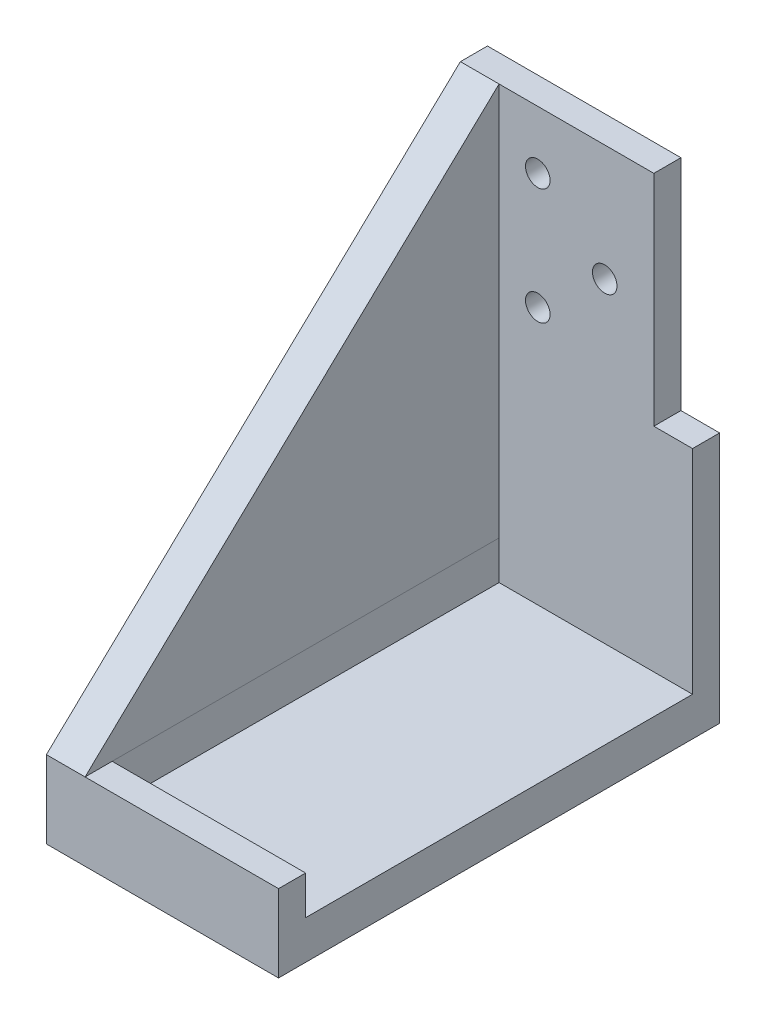
SolidWorks part; units mm, degrees
ref_plane "Front" through (0, 0, 0) normal (0, 0, 1) x (1, 0, 0)
ref_plane "Top" through (0, 0, 0) normal (0, 1, 0) x (1, 0, 0)
ref_plane "Right" through (0, 0, 0) normal (1, 0, 0) x (0, 0, -1)
sketch "Sketch1" plane through (0, 0, 0) normal (0, 1, 0) x (1, 0, 0)
  line L1 (-30, -57) -> (30, -57)
  line L2 (-30, -57) -> (-30, 57)
  line L3 (-30, 57) -> (30, 57)
  line L4 (30, -57) -> (30, 57)
  line L5 (-30, -57) -> (30, 57) construction
  line L6 (-30, 57) -> (30, -57) construction
  point P0 (0, 0)
  dimension "D1" = 60
  dimension "D2" = 114
extrude "Boss-Extrude1" add sketch "Sketch1" against normal blind 10
sketch "Sketch3" plane through (0, 0, 0) normal (0, 1, 0) x (1, 0, 0)
  line L1 (30, -57) -> (30, 57) construction
  line L5 (-30, 57) -> (30, 57)
  line L6 (30, 57) -> (-30, 57) construction
  line L7 (30, 57) -> (30, 50)
  line L8 (30, 50) -> (-30, 50)
  line L11 (-30, 50) -> (-30, 57)
  dimension "D1" = 7
extrude "Boss-Extrude2" add sketch "Sketch3" along normal offset from surface (111.6 mm away) 5
sketch "Sketch6" plane through (0, 0, 0) normal (0, 1, 0) x (1, 0, 0)
  line L0 (-30, 50) -> (-20, 50)
  line L1 (-30, 50) -> (30, 50) construction
  line L2 (-30, 50) -> (-30, -57) construction
  line L3 (-20, 50) -> (-20.1036, -50)
  line L4 (-20.1036, -50) -> (30, -50)
  line L5 (30, -50) -> (30, -57)
  line L6 (30, -57) -> (-30, -57)
  line L7 (-30, -57) -> (30, -57) construction
  line L8 (-30, -57) -> (-30, 50)
  point P13 (0, 0)
  dimension "D1" = 10
  dimension "D2" = 7
extrude "Boss-Extrude5" add sketch "Sketch6" along normal blind 10
sketch "Sketch4" plane through (-30, 0, 0) normal (-1, 0, 0) x (0, 0, 1)
  line L0 (-57, 10) -> (57, 10)
  line L1 (-57, -10) -> (-57, 111.6) construction
  line L5 (57, 10) -> (-50, 111.6)
  line L6 (-50, 111.6) -> (-50, 10) construction
  line L7 (-50, 111.6) -> (-57, 111.6)
  line L8 (-57, 111.6) -> (-57, 10)
  line L10 (-57, 111.6) -> (-50, 111.6) construction
  line L11 (57, -10) -> (57, 10) construction
  point P4 (57, 10)
  point P5 (57, 10)
  point P6 (57, 0)
  point P14 (0, 0)
  point P17 (-57, 93)
extrude "Boss-Extrude3" add sketch "Sketch4" against normal blind 10
sketch "Sketch7" plane through (0, 111.6, 0) normal (0, 1, 0) x (1, 0, 0)
  line L0 (30, 57) -> (30, 50) construction
  line L1 (30, 57) -> (20, 57)
  line L2 (30, 57) -> (30, 50)
  line L3 (30, 50) -> (20, 50)
  line L4 (20, 57) -> (20, 50)
  line L5 (-30, 57) -> (30, 57) construction
  line L6 (30, 50) -> (-20, 50) construction
  dimension "D1" = 10
extrude "Cut-Extrude1" cut sketch "Sketch7" against normal up to surface (56.6 mm away)
sketch "Sketch8" plane through (0, 0, -50) normal (0, 0, 1) x (1, 0, 0)
  line L0 (-20, 10) -> (-20, 111.6) construction
  line L1 (20, 55) -> (20, 111.6) construction
  line L2 (20, 111.6) -> (-20, 111.6) construction
  circle A0 centre (-10, 96.6) radius 3.175
  circle A1 centre (7.3, 81.6) radius 3.175
  circle A2 centre (-10, 66.6) radius 3.175
  point P6 (0, 0)
  point P7 (-10.3532, 99.3024)
  dimension "D1" = 6.35
  dimension "D2" = 10
  dimension "D3" = 12.7
  dimension "D4" = 15
  dimension "D5" = 15
  dimension "D6" = 15
extrude "Cut-Extrude2" cut sketch "Sketch8" against normal through all
